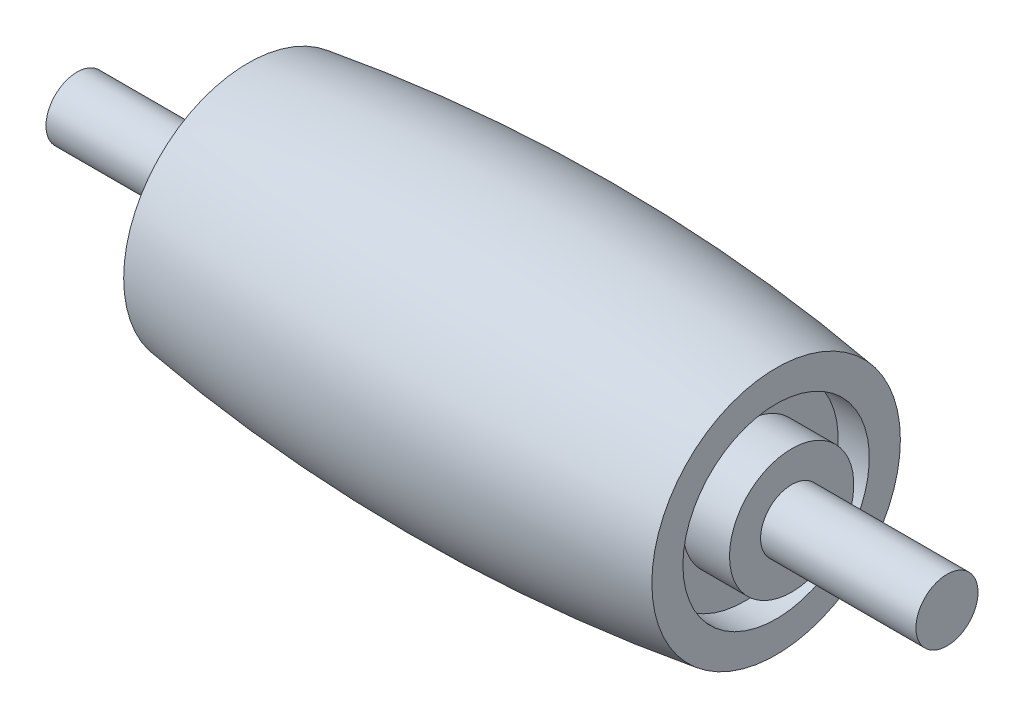
SolidWorks part; units mm, degrees
ref_plane "前视基准面" through (0, 0, 0) normal (0, 0, 1) x (1, 0, 0)
ref_plane "上视基准面" through (0, 0, 0) normal (0, 1, 0) x (1, 0, 0)
ref_plane "右视基准面" through (0, 0, 0) normal (1, 0, 0) x (0, 0, -1)
sketch "草图1" plane through (0, 0, 0) normal (0, 0, 1) x (1, 0, 0)
  line L0 (7.5136, 0) -> (24.5136, 0) construction
  line L1 (7.5136, 0) -> (7.5136, -4)
  line L2 (24.5136, 0) -> (24.5136, -4)
  line L3 (7.5136, 0) -> (24.5136, 0)
  arc A0 (7.5136, -4) -> (24.5136, -4) centre (16.0136, 54.5282) ccw
  dimension "D1" = 17
revolve "旋转2" add sketch "草图1" angle 360 about L0
sketch "草图2" plane through (7.5136, 0, 0) normal (-1, 0, 0) x (0, 0, 1)
  circle A0 centre (0, 0) radius 3
  circle A1 centre (0, 0) radius 2
extrude "切除-拉伸1" cut sketch "草图2" against normal blind 1 contours A0 | A1
sketch "草图3" plane through (7.5136, 0, 0) normal (-1, 0, 0) x (0, 0, 1)
  circle A1 centre (0, 0) radius 2
  circle A2 centre (0, 0) radius 2
  dimension "D1" = 0
extrude "凸台-拉伸1" add sketch "草图3" along normal blind 0.5
sketch "草图4" plane through (24.5136, 0, 0) normal (1, 0, 0) x (0, 0, -1)
  circle A1 centre (0, 0) radius 4
  circle A3 centre (0, 0) radius 4
  dimension "D1" = 0
sketch "草图5" plane through (7.0136, 0, 0) normal (-1, 0, 0) x (0, 0, 1)
  circle A0 centre (0, 0) radius 1
extrude "凸台-拉伸3" add sketch "草图5" along normal blind 5
cosmetic thread "装饰螺纹线1" parameters "D1"=5, "D2"=1
ref_plane "基准面5" through (16.0136, 0, 0) normal (-1, 0, 0) x (0, 0, 1)
mirror "镜向4" about plane through (16.0136, 0, 0) normal (-1, 0, 0) of "凸台-拉伸3", "凸台-拉伸1", "切除-拉伸1"
